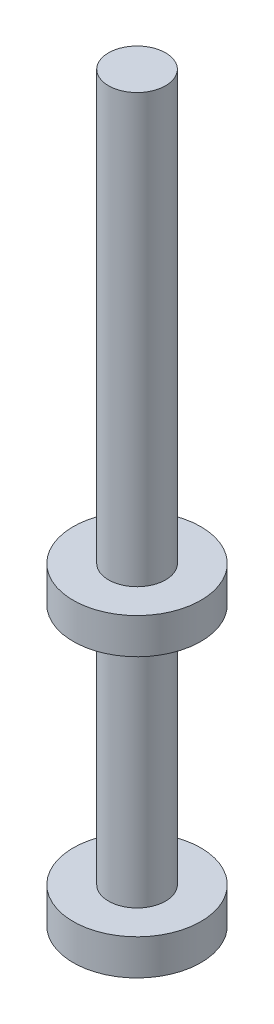
SolidWorks part; units mm, degrees
material "Liga de aço (SS)"
ref_plane "Plano frontal" through (0, 0, 0) normal (0, 0, 1) x (1, 0, 0)
ref_plane "Plano superior" through (0, 0, 0) normal (0, 1, 0) x (1, 0, 0)
ref_plane "Plano direito" through (0, 0, 0) normal (1, 0, 0) x (0, 0, -1)
sketch "Esboço1" plane through (0, 0, 0) normal (0, 0, 1) x (1, 0, 0)
  line L0 (0, 0) -> (0, 8037.7441) construction
  line L1 (0, 0) -> (8037.7441, 0) construction
  line L2 (0, 75) -> (4, 75)
  line L3 (4, 75) -> (4, 15)
  line L4 (4, 15) -> (8.95, 15)
  line L5 (8.95, 15) -> (8.95, 10)
  line L6 (8.95, 10) -> (4, 10)
  line L7 (4, 10) -> (4, -24)
  line L8 (4, -24) -> (8.95, -24)
  line L9 (8.95, -24) -> (8.95, -29)
  line L10 (8.95, -29) -> (4, -29)
  line L11 (4, -29) -> (4, -31)
  line L12 (4, -31) -> (0, -31)
  line L13 (0, -31) -> (0, 75)
  dimension "D1" = 17.9
  dimension "D2" = 60
  dimension "D3" = 5
  dimension "D4" = 8
  dimension "D5" = 2
  dimension "D6" = 10
  dimension "D7" = 24
revolve "Revolução1" add sketch "Esboço1" angle 360 about L0
